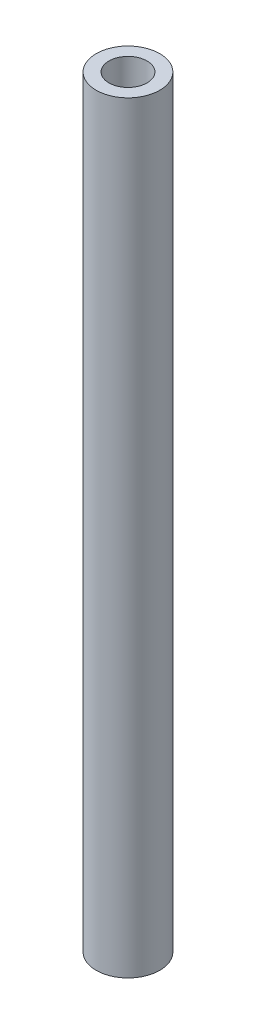
SolidWorks part; units mm, degrees
ref_plane "Front Plane" through (0, 0, 0) normal (0, 0, 1) x (1, 0, 0)
ref_plane "Top Plane" through (0, 0, 0) normal (0, 1, 0) x (1, 0, 0)
ref_plane "Right Plane" through (0, 0, 0) normal (1, 0, 0) x (0, 0, -1)
sketch "Sketch1" plane through (0, 0, 0) normal (0, 1, 0) x (1, 0, 0)
  circle A0 centre (0, 0) radius 2.5
  dimension "D1" = 5
extrude "Boss-Extrude1" add sketch "Sketch1" along normal blind 60
sketch "Sketch2" plane through (0, 60, 0) normal (0, 1, 0) x (1, 0, 0)
  circle A0 centre (0, 0) radius 1.5
  dimension "D1" = 3
extrude "Cut-Extrude1" cut sketch "Sketch2" against normal through all
